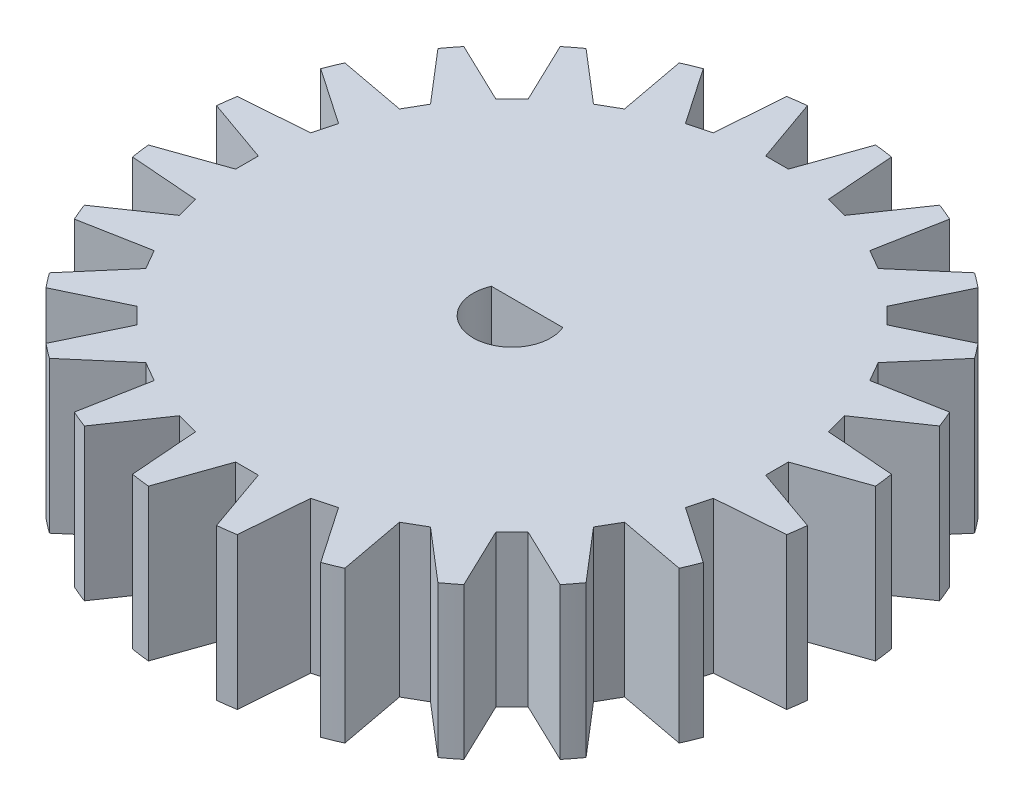
SolidWorks part; units mm, degrees
ref_plane "Front Plane" through (0, 0, 0) normal (0, 0, 1) x (1, 0, 0)
ref_plane "Top Plane" through (0, 0, 0) normal (0, 1, 0) x (1, 0, 0)
ref_plane "Right Plane" through (0, 0, 0) normal (1, 0, 0) x (0, 0, -1)
sketch "Sketch1" plane through (0, 0, 0) normal (0, 1, 0) x (1, 0, 0)
  circle A0 centre (0, 0) radius 17.5
  dimension "D1" = 35
extrude "Boss-Extrude1" add sketch "Sketch1" along normal blind 8
sketch "Sketch2" plane through (0, 8, 0) normal (0, 1, 0) x (1, 0, 0)
  line L0 (-1.8887, 0.7971) -> (1.8887, 0.7971)
  arc A0 (-1.8887, 0.7971) -> (1.8887, 0.7971) centre (0, 0) ccw
  dimension "D1" = 4.1
extrude "Cut-Extrude1" cut sketch "Sketch2" against normal through all
sketch "Sketch3" plane through (0, 8, 0) normal (0, 1, 0) x (1, 0, 0)
  line L0 (0, 0) -> (0, 14) construction
  line L1 (0, 14) -> (0.6, 14)
  line L2 (0.6, 14) -> (1.8, 17.4072)
  line L3 (1.8, 17.4072) -> (1.8, 19.3147)
  line L4 (1.8, 19.3147) -> (-1.8, 19.3147)
  line L5 (-1.8, 19.3147) -> (-1.8, 17.4072)
  line L6 (-1.8, 17.4072) -> (-0.6, 14)
  line L7 (-0.6, 14) -> (0, 14)
  circle A0 centre (0, 0) radius 17.5 construction
  dimension "D1" = 0.6
  dimension "D2" = 0.6
  dimension "D3" = 1.2
  dimension "D4" = 1.2
  dimension "D5" = 14
extrude "Cut-Extrude2" cut sketch "Sketch3" against normal blind 10
pattern_circular "CirPattern1" count 24 every 15 about axis through (0, 0, 0) along (0, 1, 0) of "Cut-Extrude2"
